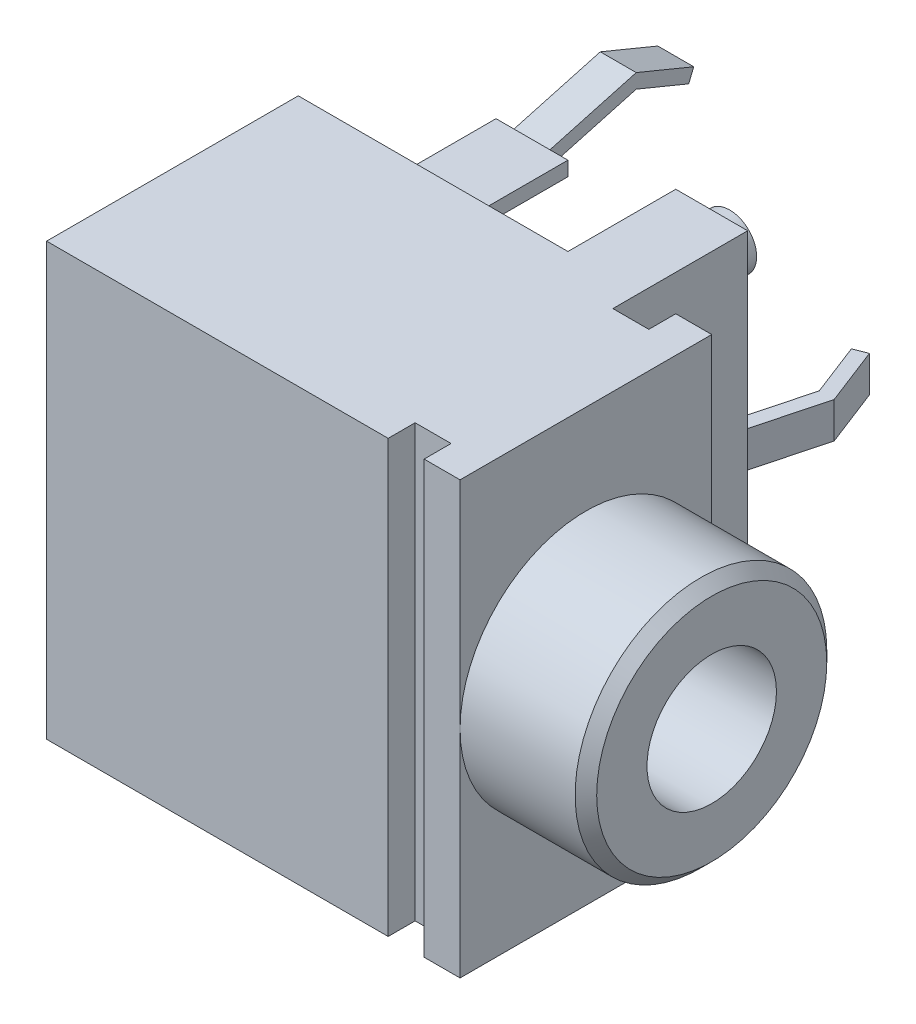
SolidWorks part; units mm, degrees
ref_plane "Plano frontal" through (0, 0, 0) normal (0, 0, 1) x (1, 0, 0)
ref_plane "Plano superior" through (0, 0, 0) normal (0, 1, 0) x (1, 0, 0)
ref_plane "Plano direito" through (0, 0, 0) normal (1, 0, 0) x (0, 0, -1)
ref_plane "Plano1" through (0, 0, -3.5) normal (0, 0, -1) x (-1, 0, 0)
sketch "Esboço1" plane through (0, 0, -3.5) normal (0, 0, -1) x (-1, 0, 0)
  line L0 (3.5, 6) -> (3.5, -6)
  line L1 (3.5, -6) -> (15, -6)
  line L2 (15, -6) -> (15, 6)
  line L3 (15, 6) -> (3.5, 6)
extrude "Ressalto-extrusão1" add sketch "Esboço1" against normal blind 7
sketch "Esboço2" plane through (0, 6, 0) normal (0, 1, 0) x (-1, 0, 0)
  line L0 (15, -2.75) -> (4.5, -2.75)
  line L1 (4.5, -2.75) -> (4.5, -3.5)
  line L2 (4.5, -3.5) -> (15, -3.5)
  line L3 (15, -3.5) -> (15, -2.75)
extrude "Corte-extrusão1" cut sketch "Esboço2" against normal through all
sketch "Esboço3" plane through (0, 0, -2.75) normal (0, 0, -1) x (-1, 0, 0)
  line L0 (15, -6) -> (5.5, -6)
  line L1 (5.5, -6) -> (5.5, 6)
  line L2 (5.5, 6) -> (15, 6)
  line L3 (15, 6) -> (15, -6)
extrude "Ressalto-extrusão2" add sketch "Esboço3" along normal blind 3.75
sketch "Esboço4" plane through (0, -6, 0) normal (0, -1, 0) x (1, 0, 0)
  line L0 (-7.5, -3.5) -> (-15, -3.5)
  line L1 (-15, -3.5) -> (-15, -6.5)
  line L2 (-15, -6.5) -> (-7.5, -6.5)
  line L3 (-7.5, -6.5) -> (-7.5, -3.5)
extrude "Corte-extrusão2" cut sketch "Esboço4" against normal through all
sketch "Esboço5" plane through (0, 0, -3.5) normal (0, 0, -1) x (-1, 0, 0)
  line L0 (12.5, -2.3) -> (12.5, -2.7)
  line L1 (12.5, -2.7) -> (10.5, -2.7)
  line L2 (10.5, -2.7) -> (10.5, -2.3)
  line L3 (10.5, -2.3) -> (12.5, -2.3)
extrude "Ressalto-extrusão3" add sketch "Esboço5" along normal blind 7
sketch "Esboço6" plane through (0, -2.7, 0) normal (0, -1, 0) x (1, 0, 0)
  line L0 (-10.5, -6.5) -> (-11, -6.5)
  line L1 (-11, -6.5) -> (-11, -10.5)
  line L2 (-11, -10.5) -> (-10.5, -10.5)
  line L3 (-10.5, -10.5) -> (-10.5, -6.5)
extrude "Corte-extrusão3" cut sketch "Esboço6" against normal through all
sketch "Esboço7" plane through (0, -2.7, 0) normal (0, -1, 0) x (1, 0, 0)
  line L0 (-12, -6.5) -> (-12.5, -6.5)
  line L1 (-12.5, -6.5) -> (-12.5, -10.5)
  line L2 (-12.5, -10.5) -> (-12, -10.5)
  line L3 (-12, -10.5) -> (-12, -6.5)
extrude "Corte-extrusão4" cut sketch "Esboço7" against normal through all
sketch "Esboço8" plane through (0, 0, -3.5) normal (0, 0, -1) x (-1, 0, 0)
  line L0 (7.5, 1) -> (12.25, 1)
  line L1 (12.25, 1) -> (12.25, -1)
  line L2 (12.25, -1) -> (7.5, -1)
  line L3 (7.5, -1) -> (7.5, 1)
extrude "Ressalto-extrusão4" add sketch "Esboço8" along normal blind 3
sketch "Esboço9" plane through (0, -6, 0) normal (0, -1, 0) x (1, 0, 0)
  line L0 (-5.5, 3.5) -> (-5.5, 2.75)
  line L1 (-5.5, 2.75) -> (-4.5, 2.75)
  line L2 (-4.5, 2.75) -> (-4.5, 3.5)
  line L3 (-4.5, 3.5) -> (-5.5, 3.5)
extrude "Corte-extrusão5" cut sketch "Esboço9" against normal through all
sketch "Esboço10" plane through (0, 0, -3.5) normal (0, 0, -1) x (-1, 0, 0)
  line L0 (10.5, 4.8) -> (10.5, 5.2)
  line L1 (10.5, 5.2) -> (12.5, 5.2)
  line L2 (12.5, 5.2) -> (12.5, 4.8)
  line L3 (12.5, 4.8) -> (10.5, 4.8)
extrude "Ressalto-extrusão5" add sketch "Esboço10" along normal blind 3
sketch "Esboço11" plane through (0, 0, -3.5) normal (0, 0, -1) x (-1, 0, 0)
  line L0 (12.5, -4.8) -> (12.5, -5.2)
  line L1 (12.5, -5.2) -> (10.5, -5.2)
  line L2 (10.5, -5.2) -> (10.5, -4.8)
  line L3 (10.5, -4.8) -> (12.5, -4.8)
extrude "Ressalto-extrusão6" add sketch "Esboço11" along normal blind 3
sketch "Esboço12" plane through (0, 0, -3.5) normal (0, 0, -1) x (-1, 0, 0)
  line L0 (12.5, 2.7) -> (12.5, 2.3)
  line L1 (12.5, 2.3) -> (10.5, 2.3)
  line L2 (10.5, 2.3) -> (10.5, 2.7)
  line L3 (10.5, 2.7) -> (12.5, 2.7)
extrude "Ressalto-extrusão7" add sketch "Esboço12" along normal blind 3
sketch "Esboço13" plane through (0, 0, -6.5) normal (0, 0, -1) x (-1, 0, 0)
  line L0 (12, 0.2) -> (12, -0.2)
  line L1 (12, -0.2) -> (11, -0.2)
  line L2 (11, -0.2) -> (11, 0.2)
  line L3 (11, 0.2) -> (12, 0.2)
extrude "Ressalto-extrusão8" add sketch "Esboço13" along normal blind 0.5
ref_plane "Plano2" through (0, -5, 0) normal (0, 1, 0) x (1, 0, 0)
sketch "Esboço14" plane through (0, -5, 0) normal (0, 1, 0) x (1, 0, 0)
  line L0 (-5.75, 7) -> (-6.5, 7)
  line L1 (-6.5, 7) -> (-6.5, 6.5)
  line L2 (-6.5, 6.5) -> (-5.75, 6.5)
  line L3 (-5.75, 6.5) -> (-5.75, 7)
  line L4 (-6.5, 7) -> (-6.5, 6.5) construction
revolve "Revolução1" add sketch "Esboço14" angle 360 about L4
ref_plane "Plano3" through (0, 5, 0) normal (0, 1, 0) x (1, 0, 0)
sketch "Esboço15" plane through (0, 5, 0) normal (0, 1, 0) x (1, 0, 0)
  line L0 (-5.75, 7) -> (-6.5, 7)
  line L1 (-6.5, 7) -> (-6.5, 6.5)
  line L2 (-6.5, 6.5) -> (-5.75, 6.5)
  line L3 (-5.75, 6.5) -> (-5.75, 7)
  line L4 (-6.5, 7) -> (-6.5, 6.5) construction
revolve "Revolução2" add sketch "Esboço15" angle 360 about L4
ref_plane "Plano4" through (0, 0, 0) normal (0, 0, -1) x (-1, 0, 0)
sketch "Esboço16" plane through (0, 0, 0) normal (0, 0, -1) x (-1, 0, 0)
  line L0 (0, 3.5) -> (0, 0)
  line L1 (0, 0) -> (3.5, 0)
  line L2 (3.5, 0) -> (3.5, 3.5)
  line L3 (3.5, 3.5) -> (0, 3.5)
  line L4 (0, 0) -> (3.5, 0) construction
revolve "Revolução3" add sketch "Esboço16" angle 360 about L4
hole_wizard "Furo de diâmetro Ø3.6 (3.6)1" positions "Esboço18" profile "Esboço17" hole size "Ø3.6" standard "Ansi Metric"
sketch "Esboço18" plane through (0, 0, 0) normal (1, 0, 0) x (0, 0, -1)
  point P0 (0, 0)
sketch "Esboço17" plane through (0, 0, 0) normal (0, 1, 0) x (0, 0, -1)
  line L0 (0, 0) -> (0, 3.5)
  line L1 (0, 3.5) -> (1.8, 3.5)
  line L2 (1.8, 3.5) -> (1.8, 0)
  line L5 (1.8, 0) -> (0, 0)
  line L10 (0, 3.5) -> (-1.8, 3.5) construction
  line L11 (0, -6.35) -> (0, 107.95) construction
  dimension "Hole Dia." = 3.6
  dimension "Hole Depth" = 3.5
  dimension "Drill Angle" = 180
chamfer "Chanfro1" distance 0.3 angle 45 1 edges at (0, 0, 3.5)
sketch "Esboço19" plane through (0, 0, -6.5) normal (0, 0, -1) x (-1, 0, 0)
  line L0 (5.5, 6) -> (5.5, -6) construction
  line L1 (6.29, -0.5) -> (6.72, -0.5)
  line L2 (6.29, -0.5) -> (6.29, 0.5)
  line L3 (6.29, 0.5) -> (6.72, 0.5)
  line L4 (6.72, -0.5) -> (6.72, 0.5)
  dimension "D1" = 1
  dimension "D2" = 0.43
  dimension "D3" = 0.79
  dimension "D4" = 0.5
extrude "Ressalto-extrusão9" add sketch "Esboço19" along normal blind 0.5
sketch "Esboço20" plane through (0, 0, 0) normal (0, 1, 0) x (1, 0, 0)
  line L0 (-6.3022, 6.9875) -> (-5.7322, 9.1375)
  line L1 (-5.7322, 9.1375) -> (-6.3522, 10.7375)
  line L2 (-6.3022, 6.9875) -> (-6.7177, 6.9875)
  line L3 (-6.3522, 10.7375) -> (-6.7134, 10.5975)
  line L4 (-6.7177, 6.9875) -> (-6.1477, 9.1375)
  line L5 (-6.1477, 9.1375) -> (-6.7134, 10.5975)
  dimension "D1" = 2.15
  dimension "D2" = 0.57
  dimension "D3" = 1.6
  dimension "D4" = 0.62
extrude "Ressalto-extrusão10" add sketch "Esboço20" along normal mid plane 1
sketch "Esboço21" plane through (-12.5, 0, 0) normal (-1, 0, 0) x (0, 0, 1)
  line L0 (-6.5, 5.2) -> (-8.9, 5.86)
  line L1 (-8.9, 5.86) -> (-10.5, 5.2)
  line L2 (-6.5, 5.2) -> (-6.5, 4.8)
  line L3 (-6.5, 4.8) -> (-8.9, 5.46)
  line L4 (-8.9, 5.46) -> (-10.359, 4.8582)
  line L5 (-10.359, 4.8582) -> (-10.5, 5.2)
  dimension "D1" = 2.4
  dimension "D2" = 1.6
  dimension "D3" = 0.66
  dimension "D4" = 0.66
extrude "Ressalto-extrusão11" add sketch "Esboço21" against normal blind 1 from offset 0.5 offset against normal yes
mirror "Espelhar1" about plane through (0, 0, 0) normal (0, 1, 0) of "Ressalto-extrusão11"
